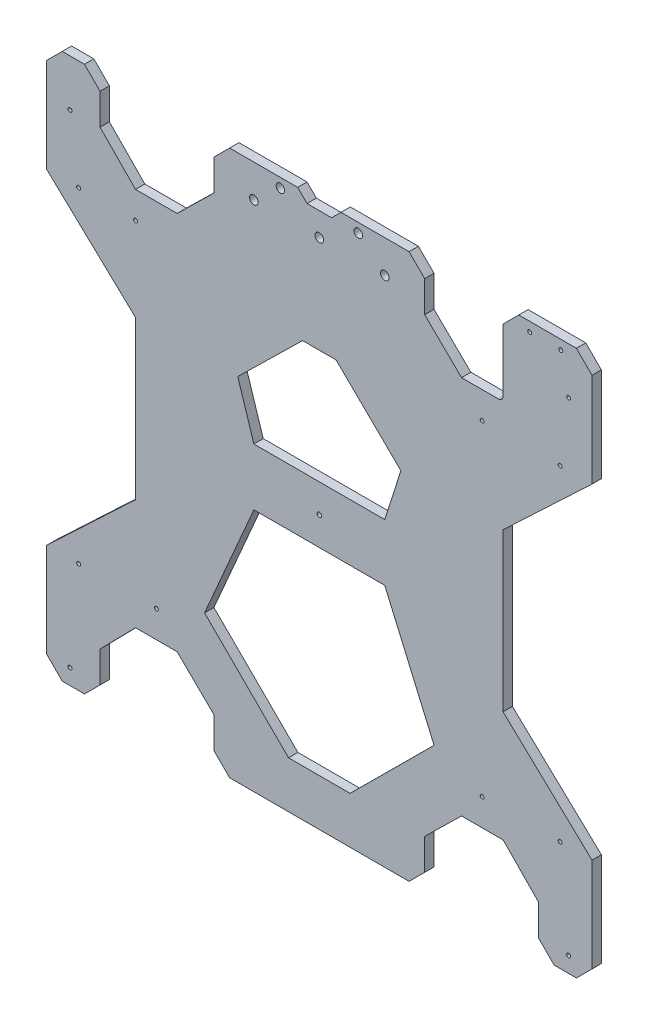
SolidWorks part; units mm, degrees
material "6063-T5"
ref_plane "Piano frontale" through (0, 0, 0) normal (0, 0, 1) x (1, 0, 0)
ref_plane "Piano superiore" through (0, 0, 0) normal (0, 1, 0) x (1, 0, 0)
ref_plane "Piano destro" through (0, 0, 0) normal (1, 0, 0) x (0, 0, -1)
sketch "Schizzo13" plane through (0, 0, 0) normal (0, 0, 1) x (1, 0, 0)
  line L0 (175, 350) -> (175, 0) construction
  line L1 (10, 0) -> (24.282, 0)
  line L2 (0, 279.5) -> (57.0808, 225.6111)
  line L3 (217, 193.2869) -> (227.343, 225.6111)
  line L4 (133, 193.2869) -> (217, 193.2869)
  line L5 (350, 175) -> (0, 175) construction
  line L6 (-60.1887, 10) -> (461.2643, 10) construction
  line L7 (279.5, 279.5) -> (279.5, 175) construction
  line L8 (-12.961, 344) -> (386.8832, 344) construction
  line L9 (-12.961, 329) -> (386.8832, 329) construction
  line L10 (161.1089, 350) -> (167.1089, 344)
  line L11 (279.5, 70.5) -> (175, 70.5) construction
  line L12 (70.5, 70.5) -> (175, 70.5) construction
  line L13 (167.1089, 344) -> (182.8911, 344)
  line L14 (57.0808, 279.5) -> (57.0808, 175) construction
  line L15 (57.0808, 279.5) -> (175, 279.5) construction
  line L16 (175, 279.5) -> (329.5, 279.5) construction
  line L17 (329.5, 70.5) -> (329.5, 279.5) construction
  line L18 (20.5, 70.5) -> (329.5, 70.5) construction
  line L19 (20.5, 70.5) -> (20.5, 279.5) construction
  line L20 (175, 279.5) -> (20.5, 279.5) construction
  line L21 (15, -40.9714) -> (15, 408.5301) construction
  line L22 (335, -40.9714) -> (335, 408.5301) construction
  line L23 (-12.961, 320) -> (386.8832, 320) construction
  line L24 (10, 0) -> (0, 10)
  line L25 (340, 0) -> (350, 10)
  line L26 (107.4046, 340) -> (107.4046, 320)
  line L27 (107.4046, 320) -> (83.7454, 296.8073)
  line L28 (57.0808, 279.5) -> (20.5, 279.5) construction
  line L29 (57.0174, 296.8073) -> (34.282, 320)
  line L30 (83.7454, 296.8073) -> (57.0174, 296.8073)
  line L31 (34.282, 320) -> (34.282, 340)
  line L32 (24.282, 350) -> (10, 350)
  line L33 (133, 193.2869) -> (122.657, 225.6111)
  line L34 (57.0808, 279.5) -> (57.0808, 350) construction
  line L35 (164.2491, 266.3832) -> (185.7509, 266.3832)
  line L36 (122.657, 225.6111) -> (164.2491, 266.3832)
  line L37 (57.0808, 225.6111) -> (57.0808, 175)
  line L38 (227.343, 225.6111) -> (185.7509, 266.3832)
  line L39 (292.9192, 225.6111) -> (292.9192, 124.3889)
  line L40 (350, 279.5) -> (292.9192, 225.6111)
  line L41 (188.8911, 350) -> (182.8911, 344)
  line L42 (117.4046, 350) -> (161.1089, 350)
  line L44 (292.9826, 299.8073) -> (292.9826, 340)
  line L46 (117.4046, 0) -> (232.5954, 0)
  line L47 (266.2546, 296.8073) -> (289.9826, 296.8073)
  line L48 (242.5954, 320) -> (266.2546, 296.8073)
  line L49 (242.5954, 340) -> (242.5954, 320)
  line L50 (350, 70.5) -> (292.9192, 124.3889)
  line L53 (350, 10) -> (350, 70.5)
  line L55 (315.718, 30) -> (315.718, 10)
  line L56 (292.9826, 53.1927) -> (315.718, 30)
  line L57 (266.2546, 53.1927) -> (292.9826, 53.1927)
  line L58 (242.5954, 30) -> (266.2546, 53.1927)
  line L59 (242.5954, 10) -> (242.5954, 30)
  line L60 (107.4046, 10) -> (107.4046, 30)
  line L61 (107.4046, 30) -> (83.7454, 53.1927)
  line L62 (83.7454, 53.1927) -> (57.0174, 53.1927)
  line L63 (57.0174, 53.1927) -> (34.282, 30)
  line L64 (34.282, 30) -> (34.282, 10)
  line L66 (0, 10) -> (0, 70.5)
  line L69 (0, 70.5) -> (57.0808, 124.3889)
  line L70 (57.0808, 124.3889) -> (57.0808, 175)
  line L71 (0, 279.5) -> (0, 340)
  line L72 (188.8911, 350) -> (232.5954, 350)
  line L73 (302.9826, 350) -> (340, 350)
  line L74 (350, 279.5) -> (350, 340)
  line L75 (325.718, 0) -> (340, 0)
  line L76 (24.282, 0) -> (34.282, 10)
  line L77 (117.4046, 0) -> (107.4046, 10)
  line L78 (232.5954, 0) -> (242.5954, 10)
  line L79 (315.718, 10) -> (325.718, 0)
  line L80 (10, 350) -> (0, 340)
  line L81 (24.282, 350) -> (34.282, 340)
  line L82 (107.4046, 340) -> (117.4046, 350)
  line L83 (232.5954, 350) -> (242.5954, 340)
  line L84 (292.9826, 340) -> (302.9826, 350)
  line L85 (340, 350) -> (350, 340)
  line L86 (133, 156.7131) -> (101.3482, 83.6168)
  line L87 (101.3482, 83.6168) -> (155.2542, 30)
  line L88 (155.2542, 30) -> (194.7458, 30)
  line L89 (133, 156.7131) -> (217, 156.7131)
  line L90 (248.6518, 83.6168) -> (194.7458, 30)
  line L91 (217, 156.7131) -> (248.6518, 83.6168)
  circle A0 centre (15, 320) radius 1.25
  circle A1 centre (20.5, 279.5) radius 1.25
  circle A2 centre (57.0808, 279.5) radius 1.25
  circle A3 centre (175, 175) radius 1.5
  arc A4 (289.9826, 296.8073) -> (292.9826, 299.8073) centre (289.9826, 299.8073) ccw
  circle A5 centre (20.5, 70.5) radius 1.25
  circle A6 centre (200, 344) radius 2.75
  circle A7 centre (150, 344) radius 2.75
  circle A8 centre (175, 329) radius 2.75
  circle A9 centre (217, 329) radius 2.75
  circle A10 centre (133, 329) radius 2.75
  circle A11 centre (70.5, 70.5) radius 1.25
  circle A12 centre (279.5, 70.5) radius 1.25
  circle A13 centre (329.5, 70.5) radius 1.25
  circle A14 centre (335, 10) radius 1.25
  circle A15 centre (15, 10) radius 1.25
  circle A16 centre (279.5, 279.5) radius 1.25
  circle A17 centre (329.5, 279.5) radius 1.25
  circle A18 centre (335, 320) radius 1.25
  circle A19 centre (310, 344) radius 1.25
  circle A20 centre (330, 344) radius 1.25
  point P7 (175, 175)
  point P25 (175, 344)
  point P30 (175, 329)
  point P41 (175, 175)
  point P43 (329.5, 175)
  point P46 (15, 320)
  point P54 (335, 320)
  point P55 (335, 10)
  point P56 (15, 10)
  point P57 (15, 320)
  point P58 (335, 320)
  point P59 (15, 10)
  point P60 (335, 10)
  point P93 (292.9826, 296.8073)
  point P108 (175, 344)
  point P155 (175, 156.7131)
  point P156 (175, 30)
  dimension "D5" = 42
  dimension "D6" = 5.5
  dimension "D7" = 25
  dimension "D8" = 15
  dimension "D10" = 154.5
  dimension "D3" = 104.5
  dimension "D17" = 20
  dimension "D2" = 3
  dimension "D9" = 2.5
  dimension "D11" = 104.5
  dimension "D12" = 175
  dimension "D13" = 6
  dimension "D15" = 310
  dimension "D16" = 320
extrude "Estrusione-Estrusione2" add sketch "Schizzo13" against normal blind 6
sketch "Schizzo14" plane through (0, 0, 0) normal (0, 0, 1) x (1, 0, 0)
  line L0 (350, 350.0234) -> (0, 350.0234)
  line L2 (0, 350.0234) -> (0, 0)
  line L3 (0, 0) -> (350, 0)
  line L4 (117.4046, 0) -> (232.5954, 0) construction
  line L5 (175, 344) -> (175, 0) construction
  line L6 (350, 350.0234) -> (350, 0)
  line L7 (182.8911, 344) -> (167.1089, 344) construction
  circle A0 centre (175, 223.4858) radius 4.4409
  circle A1 centre (175, 78.9698) radius 4.6362
  dimension "D1" = 350.0234
  dimension "D2" = 350
sketch "Schizzo15" plane through (0, 0, 0) normal (0, 0, 1) x (1, 0, 0)
  text T0 "HackerBot" font "Lobster 1.4" height 14
